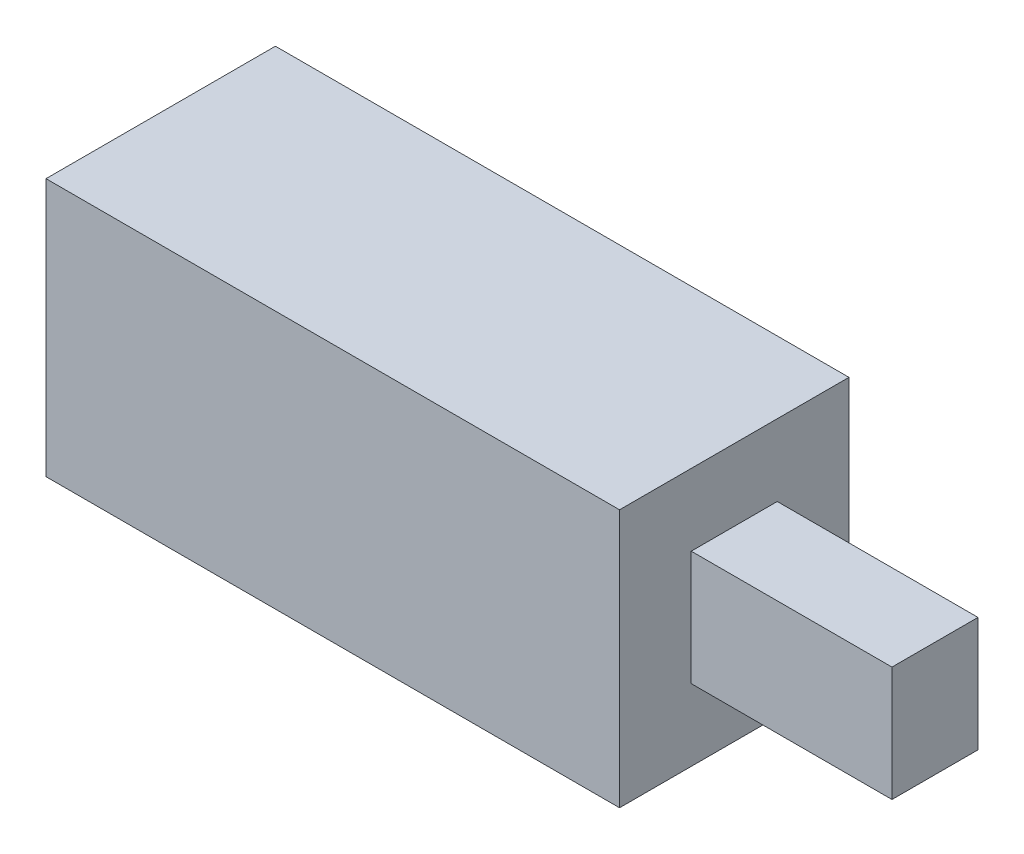
SolidWorks part; units mm, degrees
ref_plane "Front Plane" through (0, 0, 0) normal (0, 0, 1) x (1, 0, 0)
ref_plane "Top Plane" through (0, 0, 0) normal (0, 1, 0) x (1, 0, 0)
ref_plane "Right Plane" through (0, 0, 0) normal (1, 0, 0) x (0, 0, -1)
sketch "Sketch2" plane through (0, 0, 0) normal (0, 0, 1) x (1, 0, 0)
  line L1 (10, -4.5) -> (-10, -4.5)
  line L2 (10, -4.5) -> (10, 4.5)
  line L3 (10, 4.5) -> (-10, 4.5)
  line L4 (-10, -4.5) -> (-10, 4.5)
  line L5 (10, -4.5) -> (-10, 4.5) construction
  line L6 (10, 4.5) -> (-10, -4.5) construction
  point P0 (0, 0)
  dimension "D1" = 20
  dimension "D2" = 9
extrude "Boss-Extrude1" add sketch "Sketch2" along normal blind 8
sketch "Sketch3" plane through (-10, 0, 0) normal (-1, 0, 0) x (0, 0, 1)
  line L3 (2, -2.5) -> (6, -2.5)
  line L4 (2, -2.5) -> (2, 2.5)
  line L5 (2, 2.5) -> (6, 2.5)
  line L6 (6, -2.5) -> (6, 2.5)
  line L7 (2, -2.5) -> (6, 2.5) construction
  line L8 (2, 2.5) -> (6, -2.5) construction
  point P5 (4, 0)
  dimension "D1" = 4
  dimension "D2" = 5
extrude "Cut-Extrude1" cut sketch "Sketch3" against normal blind 10
sketch "Sketch4" plane through (10, 0, 0) normal (1, 0, 0) x (0, 0, -1)
  line L3 (-5.5, -2) -> (-2.5, -2)
  line L4 (-5.5, -2) -> (-5.5, 2)
  line L5 (-5.5, 2) -> (-2.5, 2)
  line L6 (-2.5, -2) -> (-2.5, 2)
  line L7 (-5.5, -2) -> (-2.5, 2) construction
  line L8 (-5.5, 2) -> (-2.5, -2) construction
  point P5 (-4, 0)
  dimension "D1" = 3
  dimension "D2" = 4
extrude "Boss-Extrude2" add sketch "Sketch4" along normal blind 7
